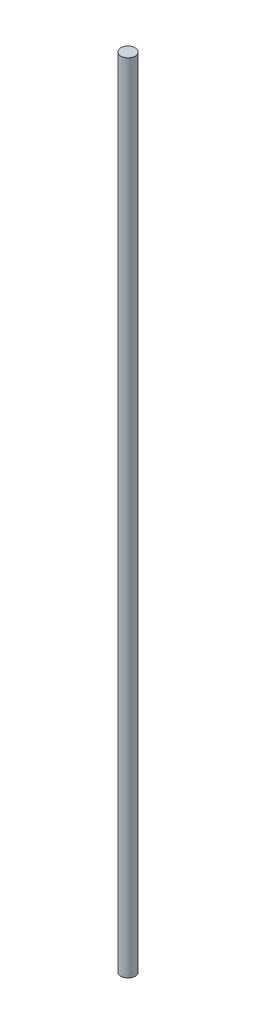
SolidWorks part; units mm, degrees
ref_plane "Front Plane" through (0, 0, 0) normal (0, 0, 1) x (1, 0, 0)
ref_plane "Top Plane" through (0, 0, 0) normal (0, 1, 0) x (1, 0, 0)
ref_plane "Right Plane" through (0, 0, 0) normal (1, 0, 0) x (0, 0, -1)
sketch "Sketch1" plane through (0, 0, 0) normal (0, 1, 0) x (1, 0, 0)
  circle A0 centre (0, 0) radius 4
  dimension "D1" = 8
extrude "Boss-Extrude1" add sketch "Sketch1" along normal blind 440
